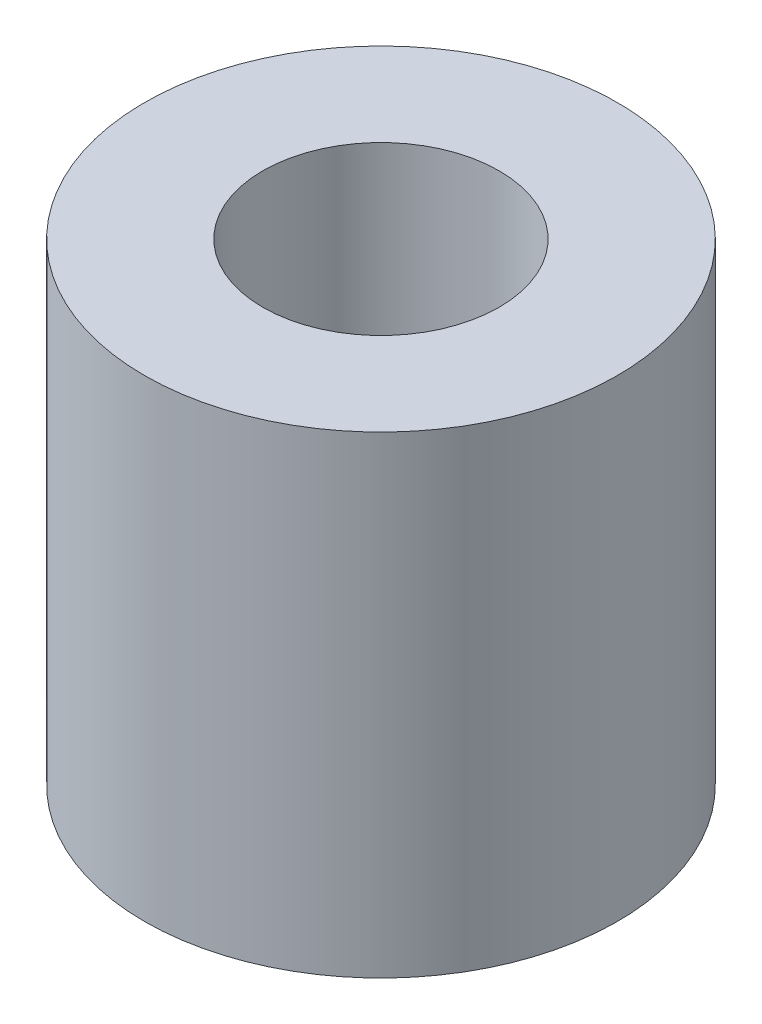
SolidWorks part; units mm, degrees
ref_plane "Front Plane" through (0, 0, 0) normal (0, 0, 1) x (1, 0, 0)
ref_plane "Top Plane" through (0, 0, 0) normal (0, 1, 0) x (1, 0, 0)
ref_plane "Right Plane" through (0, 0, 0) normal (1, 0, 0) x (0, 0, -1)
sketch "Sketch1" plane through (0, 0, 0) normal (0, 1, 0) x (1, 0, 0)
  circle A0 centre (0, 0) radius 3
  circle A1 centre (0, 0) radius 10
  dimension "D1" = 6
  dimension "D2" = 20
extrude "Boss-Extrude1" add sketch "Sketch1" along normal blind 10
sketch "Sketch2" plane through (0, 10, 0) normal (0, 1, 0) x (1, 0, 0)
  circle A0 centre (0, 0) radius 10
  circle A1 centre (0, 0) radius 5
  circle A2 centre (0, 0) radius 10 construction
  dimension "D1" = 10
extrude "Boss-Extrude2" add sketch "Sketch2" along normal blind 10
